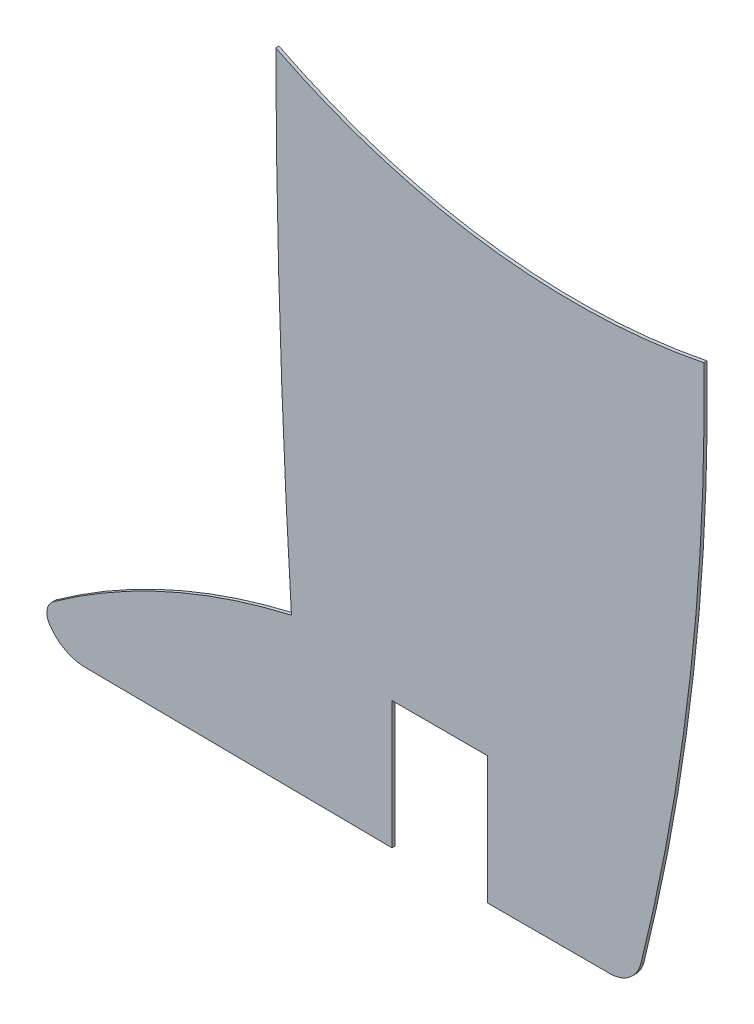
SolidWorks part; units mm, degrees
ref_plane "Alzado" through (0, 0, 0) normal (0, 0, 1) x (1, 0, 0)
ref_plane "Planta" through (0, 0, 0) normal (0, 1, 0) x (1, 0, 0)
ref_plane "Vista lateral" through (0, 0, 0) normal (1, 0, 0) x (0, 0, -1)
sketch "Model" plane through (0, 0, 0) normal (0, 0, 1) x (1, 0, 0)
  line L0 (27.4191, -46.7119) -> (17.8557, -46.6213)
  line L1 (27.4191, -42.7102) -> (27.4191, -46.7119)
  line L2 (30.4191, -42.7102) -> (27.4191, -42.7102)
  line L3 (30.4191, -46.7115) -> (30.4191, -42.7102)
  line L4 (34.258, -46.711) -> (30.4191, -46.7115)
  arc A0 (23.7725, -26.7978) -> (37.2007, -28.6384) centre (33.1492, -8.2929) ccw
  arc A1 (34.258, -46.711) -> (35.2266, -45.959) centre (34.2579, -45.711) ccw
  arc A2 (35.2266, -45.959) -> (37.2007, -28.6384) centre (-29.9983, -29.7522) ccw
  arc A3 (23.7725, -26.7978) -> (24.2644, -41.9668) centre (284.8636, -25.9235) ccw
  arc A4 (24.2644, -41.9668) -> (16.7941, -45.334) centre (28.9291, -62.2857) ccw
  arc A5 (16.7941, -45.334) -> (16.6739, -46.0125) centre (17.0908, -45.7364) ccw
  arc A6 (16.6739, -46.0125) -> (17.8557, -46.6213) centre (17.8088, -45.261) ccw
extrude "Saliente-Extruir1" add sketch "Model" along normal blind 0.1
